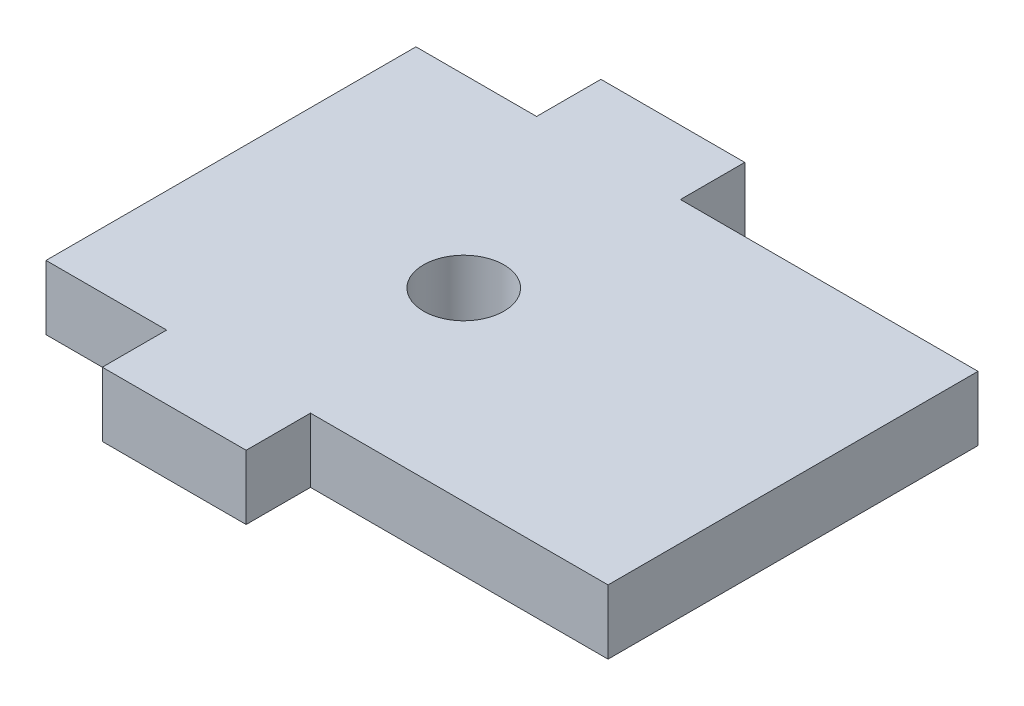
SolidWorks part; units mm, degrees
ref_plane "Front Plane" through (0, 0, 0) normal (0, 0, 1) x (1, 0, 0)
ref_plane "Top Plane" through (0, 0, 0) normal (0, 1, 0) x (1, 0, 0)
ref_plane "Right Plane" through (0, 0, 0) normal (1, 0, 0) x (0, 0, -1)
sketch "Sketch1" plane through (0, 0, 0) normal (0, 1, 0) x (1, 0, 0)
  line L1 (15.2044, 14.605) -> (-15.2044, 14.605)
  line L2 (15.2044, 14.605) -> (15.2044, -14.605)
  line L3 (15.2044, -14.605) -> (-15.2044, -14.605)
  line L4 (-15.2044, 14.605) -> (-15.2044, -14.605)
  line L5 (15.2044, 14.605) -> (-15.2044, -14.605) construction
  line L6 (15.2044, -14.605) -> (-15.2044, 14.605) construction
  line L7 (-5.6794, 14.605) -> (5.6794, 14.605)
  line L8 (-5.6794, 14.605) -> (-5.6794, 19.685)
  line L9 (-5.6794, 19.685) -> (5.6794, 19.685)
  line L10 (5.6794, 14.605) -> (5.6794, 19.685)
  line L11 (-5.6794, -14.605) -> (5.6794, -14.605)
  line L12 (-5.6794, -14.605) -> (-5.6794, -19.685)
  line L13 (-5.6794, -19.685) -> (5.6794, -19.685)
  line L14 (5.6794, -14.605) -> (5.6794, -19.685)
  point P0 (0, 0)
  point P16 (0, 14.605)
  dimension "D1" = 30.4089
  dimension "D2" = 29.21
  dimension "D3" = 5.08
  dimension "D4" = 9.525
extrude "Boss-Extrude1" add sketch "Sketch1" along normal blind 5.08 contours L1 L4 L3 L2 | L1 L10 L9 L8 | L14 L3 L12 L13
hole_wizard "1/4 (0.25) Diameter Hole1" positions "Sketch2" profile "Sketch4" hole size "1/4" standard "ANSI Inch" end condition through all
sketch "Sketch2" plane through (0, 5.08, 0) normal (0, 1, 0) x (1, 0, 0)
  point P0 (3.175, 0)
  dimension "D1" = 3.175
sketch "Sketch4" plane through (3.175, 5.08, 0) normal (1, 0, 0) x (0, 0, 1)
  line L0 (0, 0) -> (0, 5.08)
  line L1 (0, 5.08) -> (3.175, 5.08)
  line L2 (3.175, 5.08) -> (3.175, 0)
  line L5 (3.175, 0) -> (0, 0)
  line L11 (0, -6.35) -> (0, 107.95) construction
  dimension "Thru Hole Dia." = 6.35
  dimension "Thru Hole Depth" = 5.08
sketch "Sketch5" plane through (0, 5.08, 0) normal (0, 1, 0) x (1, 0, 0)
  line L0 (15.2044, 14.605) -> (15.2044, -14.605)
  line L1 (15.2044, 14.605) -> (29.1744, 14.605)
  line L2 (15.2044, -14.605) -> (29.1744, -14.605)
  line L3 (29.1744, 14.605) -> (29.1744, -14.605)
  dimension "D1" = 13.97
extrude "Boss-Extrude2" add sketch "Sketch5" against normal up to surface (5.08 mm away) up to face at (3.175, 0, 3.175)
equation "\"D1@Sketch1\"=1.125/cos(20)"
